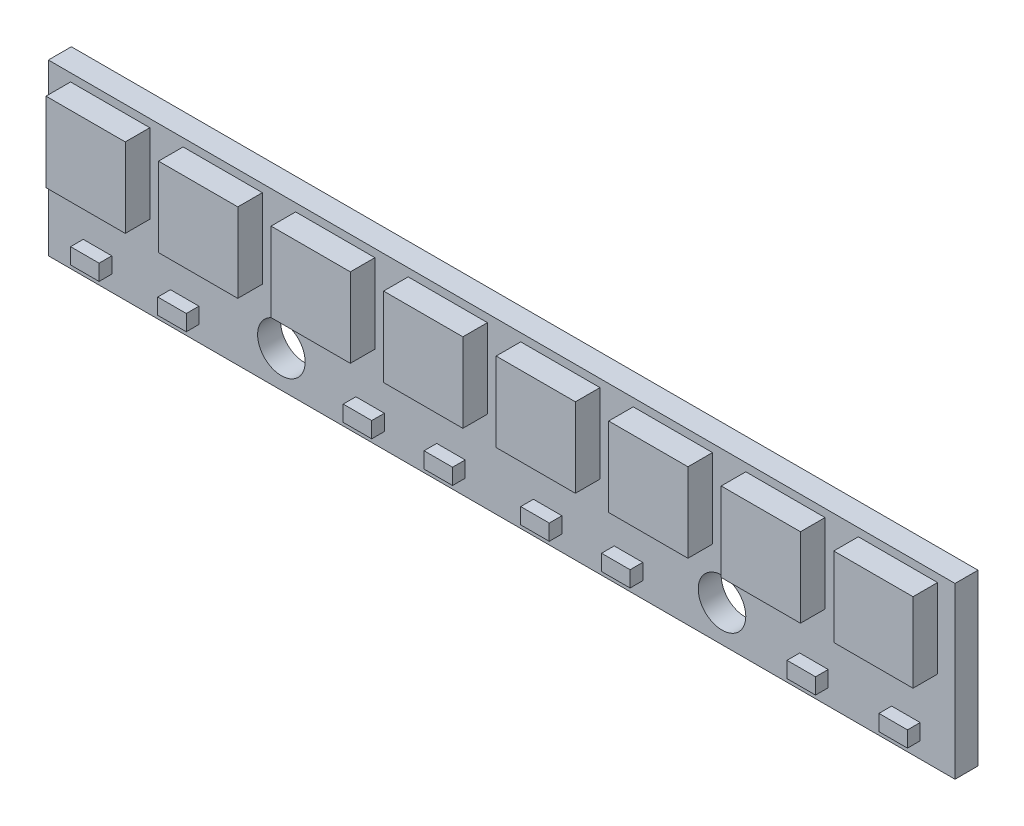
SolidWorks part; units mm, degrees
ref_plane "Alzado" through (0, 0, 0) normal (0, 0, 1) x (1, 0, 0)
ref_plane "Planta" through (0, 0, 0) normal (0, 1, 0) x (1, 0, 0)
ref_plane "Vista lateral" through (0, 0, 0) normal (1, 0, 0) x (0, 0, -1)
sketch "Croquis1" plane through (0, 0, 0) normal (0, 0, 1) x (1, 0, 0)
  line L1 (0, 0) -> (57.2, 0)
  line L2 (0, 0) -> (0, 10.7)
  line L3 (0, 10.7) -> (57.2, 10.7)
  line L4 (57.2, 0) -> (57.2, 10.7)
  dimension "D1" = 57.2
  dimension "D2" = 10.7
extrude "Saliente-Extruir1" add sketch "Croquis1" along normal blind 1.45
sketch "Croquis2" plane through (0, 0, 1.45) normal (0, 0, 1) x (1, 0, 0)
  line L0 (0, 10.7) -> (0, 0) construction
  line L1 (1.4, 10.2) -> (6.4, 10.2)
  line L2 (1.4, 10.2) -> (1.4, 5.2)
  line L3 (1.4, 5.2) -> (6.4, 5.2)
  line L4 (6.4, 10.2) -> (6.4, 5.2)
  line L5 (57.2, 10.7) -> (0, 10.7) construction
  dimension "D1" = 5
  dimension "D2" = 1.4
  dimension "D3" = 0.5
extrude "Saliente-Extruir2" add sketch "Croquis2" along normal blind 1.55
pattern_linear "MatrizL1" count 8 spacing 7.1 along (1, 0, 0) of "Saliente-Extruir2"
sketch "Croquis3" plane through (0, 0, 1.45) normal (0, 0, 1) x (1, 0, 0)
  line L0 (0, 10.7) -> (0, 0) construction
  line L1 (57.2, 0) -> (57.2, 10.7) construction
  line L2 (57.2, 10.7) -> (0, 10.7) construction
  circle A0 centre (14.7, 2.3) radius 1.5
  circle A1 centre (42.5, 2.3) radius 1.5
  dimension "D1" = 3
  dimension "D2" = 14.7
  dimension "D3" = 14.7
  dimension "D4" = 8.4
extrude "Cortar-Extruir1" cut sketch "Croquis3" against normal up to next
sketch "Croquis4" plane through (0, 0, 1.45) normal (0, 0, 1) x (1, 0, 0)
  line L0 (0, 1) -> (57.2, 1) construction
  line L1 (0, 10.7) -> (0, 0) construction
  line L2 (57.2, 0) -> (57.2, 10.7) construction
  line L3 (0, 0) -> (57.2, 0) construction
  line L4 (2.2, 1) -> (4, 1)
  line L5 (2.2, 1) -> (2.2, 2)
  line L6 (2.2, 2) -> (4, 2)
  line L7 (4, 1) -> (4, 2)
  line L8 (9.5, 1) -> (7.7, 1)
  line L9 (9.5, 1) -> (9.5, 2)
  line L10 (9.5, 2) -> (7.7, 2)
  line L11 (7.7, 1) -> (7.7, 2)
  line L12 (19.4, 1) -> (21.2, 1)
  line L13 (19.4, 1) -> (19.4, 2)
  line L14 (19.4, 2) -> (21.2, 2)
  line L15 (21.2, 1) -> (21.2, 2)
  line L16 (24.5, 1) -> (26.3, 1)
  line L17 (24.5, 1) -> (24.5, 2)
  line L18 (24.5, 2) -> (26.3, 2)
  line L19 (26.3, 1) -> (26.3, 2)
  line L20 (30.6, 1) -> (32.4, 1)
  line L21 (30.6, 1) -> (30.6, 2)
  line L22 (30.6, 2) -> (32.4, 2)
  line L23 (32.4, 1) -> (32.4, 2)
  line L24 (35.7, 1) -> (37.5, 1)
  line L25 (35.7, 1) -> (35.7, 2)
  line L26 (35.7, 2) -> (37.5, 2)
  line L27 (37.5, 1) -> (37.5, 2)
  line L28 (47.4, 1) -> (49.2, 1)
  line L29 (47.4, 1) -> (47.4, 2)
  line L30 (47.4, 2) -> (49.2, 2)
  line L31 (49.2, 1) -> (49.2, 2)
  line L32 (53.2, 1) -> (55, 1)
  line L33 (53.2, 1) -> (53.2, 2)
  line L34 (53.2, 2) -> (55, 2)
  line L35 (55, 1) -> (55, 2)
  dimension "D1" = 1
  dimension "D2" = 4
  dimension "D3" = 1.8
  dimension "D4" = 9.8
  dimension "D5" = 1
  dimension "D6" = 3.3
  dimension "D7" = 4.3
  dimension "D8" = 3.3
  dimension "D9" = 9.9
  dimension "D10" = 9.9
  dimension "D11" = 4
extrude "Saliente-Extruir3" add sketch "Croquis4" along normal blind 0.8
